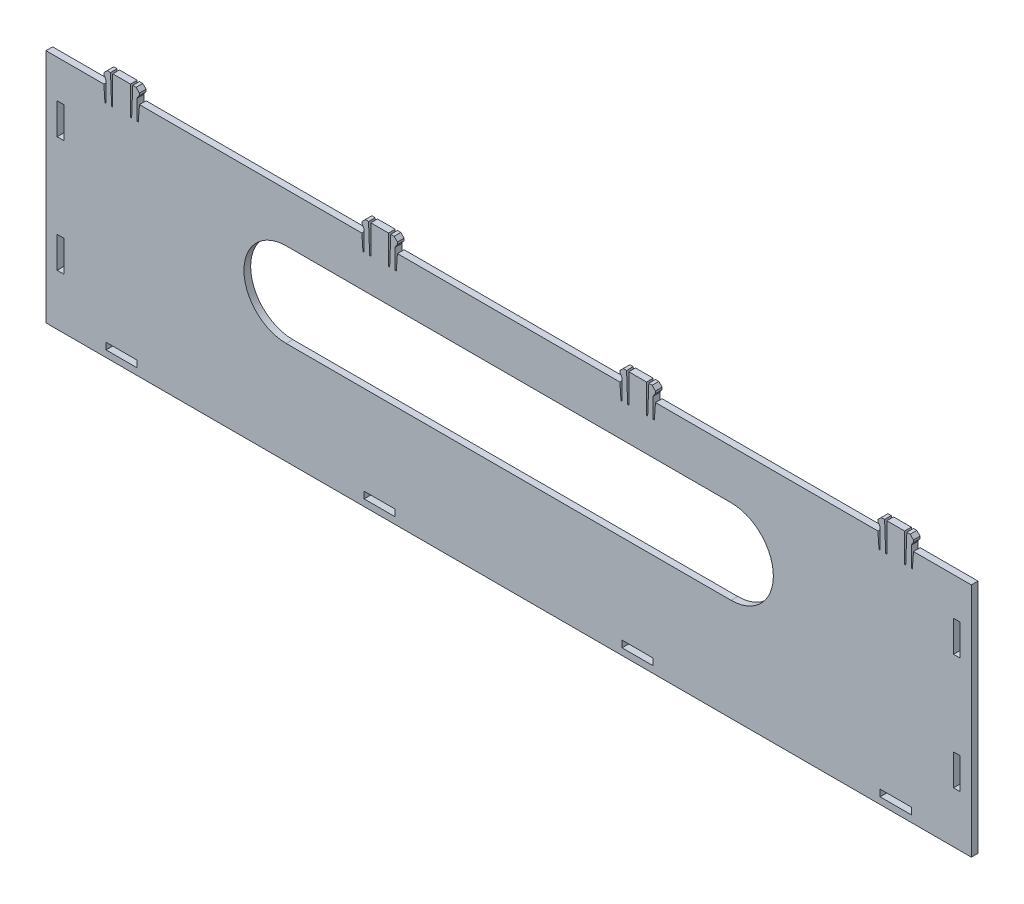
SolidWorks part; units mm, degrees
ref_plane "Front Plane" through (0, 0, 0) normal (0, 0, 1) x (1, 0, 0)
ref_plane "Top Plane" through (0, 0, 0) normal (0, 1, 0) x (1, 0, 0)
ref_plane "Right Plane" through (0, 0, 0) normal (1, 0, 0) x (0, 0, -1)
sketch "Sketch1" plane through (0, 0, 0) normal (0, 0, 1) x (1, 0, 0)
  line L0 (208, 50) -> (182, 50)
  line L1 (-208, 50) -> (-182, 50)
  line L2 (-208, 50) -> (-208, -56)
  line L3 (-208, -56) -> (208, -56)
  line L4 (208, 50) -> (208, -56)
  line L7 (-166, 50) -> (-66, 50)
  line L8 (-50, 50) -> (50, 50)
  line L9 (166, 50) -> (66, 50)
  line L10 (-182, 50) -> (-181.5, 42.9978)
  line L11 (-181.5, 42.9978) -> (-181, 42.9978)
  line L12 (-181, 42.9978) -> (-181, 51.9978)
  line L13 (-181, 51.9978) -> (-181.5, 52.9978)
  line L14 (-181.5, 52.9978) -> (-182, 53.4978)
  line L15 (-182, 53.4978) -> (-182, 54.4978)
  line L16 (-182, 54.4978) -> (-180.5, 55.9978)
  line L17 (-180.5, 55.9978) -> (-179, 55.9978)
  line L18 (-179, 55.9978) -> (-178.5, 42.9978)
  line L19 (-178.5, 42.9978) -> (-178, 42.9978)
  line L20 (-178, 42.9978) -> (-178, 55.9978)
  line L21 (-174, 50) -> (-174, 55.7386) construction
  line L22 (-170, 42.9978) -> (-170, 55.9978)
  line L23 (-169.5, 42.9978) -> (-170, 42.9978)
  line L24 (-169, 55.9978) -> (-169.5, 42.9978)
  line L25 (-167.5, 55.9978) -> (-169, 55.9978)
  line L26 (-166, 54.4978) -> (-167.5, 55.9978)
  line L27 (-166, 53.4978) -> (-166, 54.4978)
  line L28 (-166.5, 52.9978) -> (-166, 53.4978)
  line L29 (-167, 51.9978) -> (-166.5, 52.9978)
  line L30 (-167, 42.9978) -> (-167, 51.9978)
  line L31 (-166.5, 42.9978) -> (-167, 42.9978)
  line L32 (-166, 50) -> (-166.5, 42.9978)
  line L33 (-178, 55.9978) -> (-170, 55.9978)
  line L34 (-66, 50) -> (-65.5, 42.9978)
  line L35 (-65.5, 42.9978) -> (-65, 42.9978)
  line L36 (-65, 42.9978) -> (-65, 51.9978)
  line L37 (-65, 51.9978) -> (-65.5, 52.9978)
  line L38 (-65.5, 52.9978) -> (-66, 53.4978)
  line L39 (-66, 53.4978) -> (-66, 54.4978)
  line L40 (-66, 54.4978) -> (-64.5, 55.9978)
  line L41 (-64.5, 55.9978) -> (-63, 55.9978)
  line L42 (-63, 55.9978) -> (-62.5, 42.9978)
  line L43 (-62.5, 42.9978) -> (-62, 42.9978)
  line L44 (-62, 42.9978) -> (-62, 55.9978)
  line L45 (-58, 50) -> (-58, 55.7386) construction
  line L46 (-54, 42.9978) -> (-54, 55.9978)
  line L47 (-53.5, 42.9978) -> (-54, 42.9978)
  line L48 (-53, 55.9978) -> (-53.5, 42.9978)
  line L49 (-51.5, 55.9978) -> (-53, 55.9978)
  line L50 (-50, 54.4978) -> (-51.5, 55.9978)
  line L51 (-50, 53.4978) -> (-50, 54.4978)
  line L52 (-50.5, 52.9978) -> (-50, 53.4978)
  line L53 (-51, 51.9978) -> (-50.5, 52.9978)
  line L54 (-51, 42.9978) -> (-51, 51.9978)
  line L55 (-50.5, 42.9978) -> (-51, 42.9978)
  line L56 (-50, 50) -> (-50.5, 42.9978)
  line L57 (-62, 55.9978) -> (-54, 55.9978)
  line L58 (50, 50) -> (50.5, 42.9978)
  line L59 (50.5, 42.9978) -> (51, 42.9978)
  line L60 (51, 42.9978) -> (51, 51.9978)
  line L61 (51, 51.9978) -> (50.5, 52.9978)
  line L62 (50.5, 52.9978) -> (50, 53.4978)
  line L63 (50, 53.4978) -> (50, 54.4978)
  line L64 (50, 54.4978) -> (51.5, 55.9978)
  line L65 (51.5, 55.9978) -> (53, 55.9978)
  line L66 (53, 55.9978) -> (53.5, 42.9978)
  line L67 (53.5, 42.9978) -> (54, 42.9978)
  line L68 (54, 42.9978) -> (54, 55.9978)
  line L69 (58, 50) -> (58, 55.7386) construction
  line L70 (62, 42.9978) -> (62, 55.9978)
  line L71 (62.5, 42.9978) -> (62, 42.9978)
  line L72 (63, 55.9978) -> (62.5, 42.9978)
  line L73 (64.5, 55.9978) -> (63, 55.9978)
  line L74 (66, 54.4978) -> (64.5, 55.9978)
  line L75 (66, 53.4978) -> (66, 54.4978)
  line L76 (65.5, 52.9978) -> (66, 53.4978)
  line L77 (65, 51.9978) -> (65.5, 52.9978)
  line L78 (65, 42.9978) -> (65, 51.9978)
  line L79 (65.5, 42.9978) -> (65, 42.9978)
  line L80 (66, 50) -> (65.5, 42.9978)
  line L81 (54, 55.9978) -> (62, 55.9978)
  line L82 (166, 50) -> (166.5, 42.9978)
  line L83 (166.5, 42.9978) -> (167, 42.9978)
  line L84 (167, 42.9978) -> (167, 51.9978)
  line L85 (167, 51.9978) -> (166.5, 52.9978)
  line L86 (166.5, 52.9978) -> (166, 53.4978)
  line L87 (166, 53.4978) -> (166, 54.4978)
  line L88 (166, 54.4978) -> (167.5, 55.9978)
  line L89 (167.5, 55.9978) -> (169, 55.9978)
  line L90 (169, 55.9978) -> (169.5, 42.9978)
  line L91 (169.5, 42.9978) -> (170, 42.9978)
  line L92 (170, 42.9978) -> (170, 55.9978)
  line L93 (174, 50) -> (174, 55.7386) construction
  line L94 (178, 42.9978) -> (178, 55.9978)
  line L95 (178.5, 42.9978) -> (178, 42.9978)
  line L96 (179, 55.9978) -> (178.5, 42.9978)
  line L97 (180.5, 55.9978) -> (179, 55.9978)
  line L98 (182, 54.4978) -> (180.5, 55.9978)
  line L99 (182, 53.4978) -> (182, 54.4978)
  line L100 (181.5, 52.9978) -> (182, 53.4978)
  line L101 (181, 51.9978) -> (181.5, 52.9978)
  line L102 (181, 42.9978) -> (181, 51.9978)
  line L103 (181.5, 42.9978) -> (181, 42.9978)
  line L104 (182, 50) -> (181.5, 42.9978)
  line L105 (170, 55.9978) -> (178, 55.9978)
  point P16 (-182, 50)
  point P41 (-66, 50)
  point P66 (50, 50)
  point P91 (166, 50)
  dimension "D1" = 416
  dimension "D2" = 106
  dimension "D5" = 26
  dimension "D6" = 100
  dimension "D7" = 100
  dimension "D8" = 100
  dimension "D9" = 0.5
  dimension "D10" = 9
  dimension "D11" = 0.5
  dimension "D12" = 1
  dimension "D13" = 0.5
  dimension "D14" = 0.5
  dimension "D15" = 1
  dimension "D16" = 1.5
  dimension "D17" = 1.5
  dimension "D18" = 0.5
  dimension "D19" = 0.5
  dimension "D20" = 13
  dimension "D21" = 7.0022
  dimension "D22" = 0.5
  dimension "D23" = 1.5
  dimension "D24" = 13
  dimension "D25" = 8
  dimension "D26" = 8
  dimension "D27" = 0.5
  dimension "D28" = 9
  dimension "D29" = 0.5
  dimension "D30" = 1
  dimension "D31" = 0.5
  dimension "D32" = 0.5
  dimension "D33" = 1
  dimension "D34" = 1.5
  dimension "D35" = 1.5
  dimension "D36" = 0.5
  dimension "D37" = 0.5
  dimension "D38" = 13
  dimension "D39" = 7.0022
  dimension "D40" = 0.5
  dimension "D41" = 1.5
  dimension "D42" = 13
  dimension "D43" = 8
  dimension "D44" = 8
  dimension "D45" = 0.5
  dimension "D46" = 9
  dimension "D47" = 0.5
  dimension "D48" = 1
  dimension "D49" = 0.5
  dimension "D50" = 0.5
  dimension "D51" = 1
  dimension "D52" = 1.5
  dimension "D53" = 1.5
  dimension "D54" = 0.5
  dimension "D55" = 0.5
  dimension "D56" = 13
  dimension "D57" = 7.0022
  dimension "D58" = 0.5
  dimension "D59" = 1.5
  dimension "D60" = 13
  dimension "D61" = 8
  dimension "D62" = 8
  dimension "D63" = 0.5
  dimension "D64" = 9
  dimension "D65" = 0.5
  dimension "D66" = 1
  dimension "D67" = 0.5
  dimension "D68" = 0.5
  dimension "D69" = 1
  dimension "D70" = 1.5
  dimension "D71" = 1.5
  dimension "D72" = 0.5
  dimension "D73" = 0.5
  dimension "D74" = 13
  dimension "D75" = 7.0022
  dimension "D76" = 0.5
  dimension "D77" = 1.5
  dimension "D78" = 13
  dimension "D79" = 8
  dimension "D80" = 8
  dimension "D81" = 50
  dimension "D82" = 208
extrude "Boss-Extrude1" add sketch "Sketch1" along normal blind 3
sketch "Sketch4" plane through (0, 0, 3) normal (0, 0, 1) x (1, 0, 0)
  line L0 (-100, 9) -> (100, 9) construction
  line L1 (-100, 28) -> (100, 28)
  line L2 (-100, -10) -> (100, -10)
  line L3 (-208, -56) -> (208, -56) construction
  line L4 (208, -56) -> (208, 50) construction
  arc A0 (-100, 28) -> (-100, -10) centre (-100, 9) ccw
  arc A1 (100, -10) -> (100, 28) centre (100, 9) ccw
  point P2 (0, 9)
  dimension "D1" = 38
  dimension "D2" = 46
  dimension "D3" = 200
  dimension "D4" = 208
extrude "Cut-Extrude2" cut sketch "Sketch4" against normal through all
sketch "Sketch8" plane through (0, 0, 3) normal (0, 0, 1) x (1, 0, 0)
  line L0 (0, 0) -> (0, -56) construction
  line L1 (-208, -56) -> (208, -56) construction
  line L2 (181, -50) -> (181, -53)
  line L3 (-181, -50) -> (-167, -50)
  line L4 (-181, -50) -> (-181, -53)
  line L5 (-181, -53) -> (-167, -53)
  line L6 (-167, -50) -> (-167, -53)
  line L7 (181, -50) -> (167, -50)
  line L8 (167, -50) -> (167, -53)
  line L9 (181, -53) -> (167, -53)
  line L10 (65, -50) -> (65, -53)
  line L11 (-65, -50) -> (-51, -50)
  line L12 (-65, -50) -> (-65, -53)
  line L13 (-65, -53) -> (-51, -53)
  line L14 (-51, -50) -> (-51, -53)
  line L15 (65, -50) -> (51, -50)
  line L16 (51, -50) -> (51, -53)
  line L17 (65, -53) -> (51, -53)
  dimension "D1" = 14
  dimension "D2" = 3
  dimension "D3" = 167
  dimension "D4" = 50
  dimension "D5" = 14
  dimension "D6" = 3
  dimension "D7" = 51
  dimension "D8" = 50
extrude "Cut-Extrude3" cut sketch "Sketch8" against normal blind 3
sketch "Sketch9" plane through (0, 0, 3) normal (0, 0, 1) x (1, 0, 0)
  line L0 (0, 50) -> (0, -56) construction
  line L1 (50, 50) -> (-50, 50) construction
  line L2 (-208, -56) -> (208, -56) construction
  line L3 (203, 33) -> (203, 19)
  line L4 (-203, 33) -> (-200, 33)
  line L5 (-203, 33) -> (-203, 19)
  line L6 (-203, 19) -> (-200, 19)
  line L7 (-200, 33) -> (-200, 19)
  line L8 (203, 33) -> (200, 33)
  line L9 (200, 33) -> (200, 19)
  line L10 (203, 19) -> (200, 19)
  line L12 (-203, -19) -> (-200, -19)
  line L13 (-203, -19) -> (-203, -33)
  line L14 (-203, -33) -> (-200, -33)
  line L15 (-200, -19) -> (-200, -33)
  line L16 (200, -19) -> (203, -19)
  line L17 (200, -19) -> (200, -33)
  line L18 (200, -33) -> (203, -33)
  line L19 (203, -19) -> (203, -33)
  dimension "D1" = 3
  dimension "D2" = 14
  dimension "D3" = 200
  dimension "D4" = 19
  dimension "D5" = 14
  dimension "D6" = 3
  dimension "D7" = 200
  dimension "D8" = 19
  dimension "D9" = 14
  dimension "D10" = 3
  dimension "D11" = 19
  dimension "D12" = 200
extrude "Cut-Extrude4" cut sketch "Sketch9" against normal blind 3
sketch "Sketch10" plane through (0, 0, 3) normal (0, 0, 1) x (1, 0, 0)
  text T0 "BOXY1" font "Century Gothic" height in points 22
  dimension "D1" = 14.25
  dimension "D2" = 22.5
